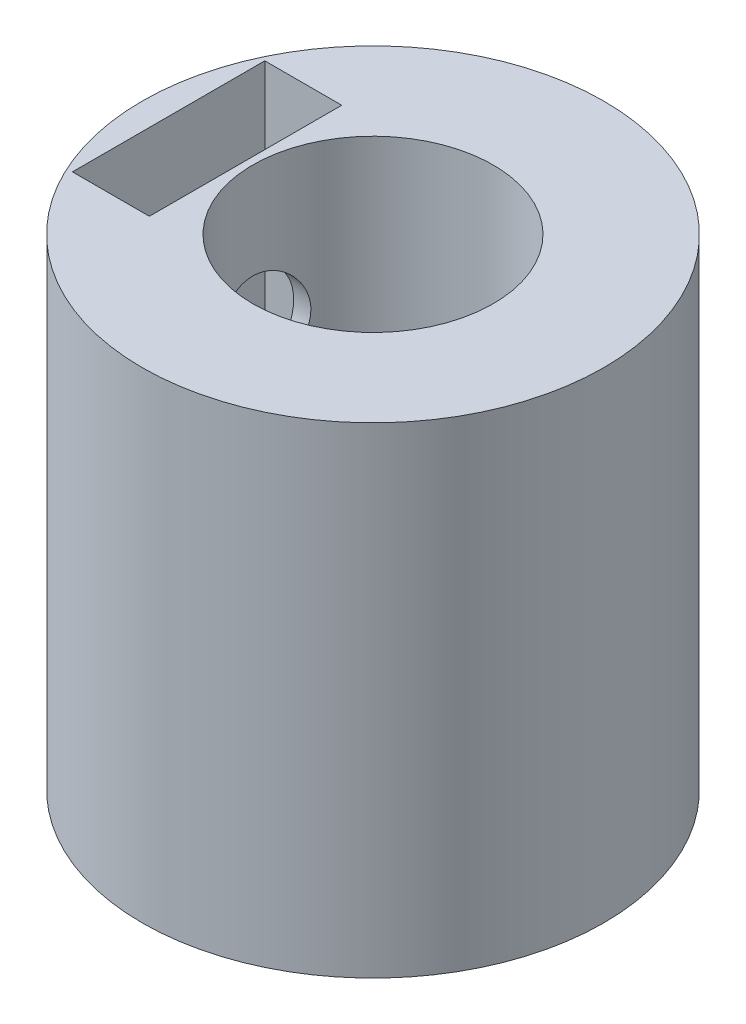
SolidWorks part; units mm, degrees
ref_plane "Ön Düzlem" through (0, 0, 0) normal (0, 0, 1) x (1, 0, 0)
ref_plane "Üst Düzlem" through (0, 0, 0) normal (0, 1, 0) x (1, 0, 0)
ref_plane "Sağ Düzlem" through (0, 0, 0) normal (1, 0, 0) x (0, 0, -1)
sketch "Çizim1" plane through (0, 0, 0) normal (0, 1, 0) x (1, 0, 0)
  circle A0 centre (0, 0) radius 4.8
  dimension "D1" = 9.6
extrude "Yükseklik-Ekstrüzyon1" add sketch "Çizim1" along normal blind 10
sketch "Çizim2" plane through (0, 10, 0) normal (0, 1, 0) x (1, 0, 0)
  circle A0 centre (0, 0) radius 2.5
  dimension "D1" = 5
extrude "Kes-Ekstrüzyon1" cut sketch "Çizim2" against normal blind 7
sketch "Çizim3" plane through (0, 0, 0) normal (1, 0, 0) x (0, 0, -1)
  line L0 (2.5, 10) -> (-2.5, 10) construction
  circle A0 centre (0, 7) radius 1
  dimension "D1" = 2
  dimension "D2" = 3
extrude "Kes-Ekstrüzyon2" cut sketch "Çizim3" against normal through all
sketch "Çizim4" plane through (0, 10, 0) normal (0, 1, 0) x (1, 0, 0)
  line L1 (-4.25, 2) -> (-2.65, 2)
  line L2 (-4.25, 2) -> (-4.25, -2)
  line L3 (-4.25, -2) -> (-2.65, -2)
  line L4 (-2.65, 2) -> (-2.65, -2)
  point P4 (-2.65, 0)
  dimension "D1" = 4
  dimension "D2" = 1.6
  dimension "D3" = 2.65
extrude "Kes-Ekstrüzyon3" cut sketch "Çizim4" against normal blind 5
